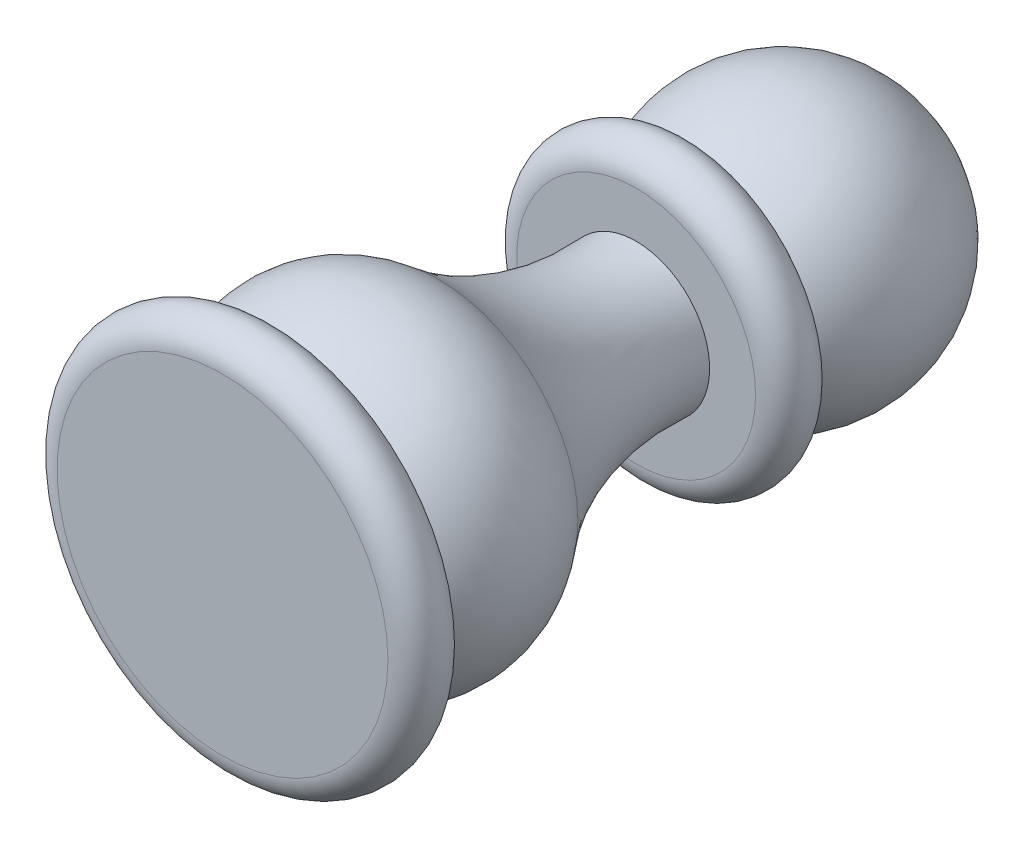
SolidWorks part; units mm, degrees
ref_plane "Front Plane" through (0, 0, 0) normal (0, 0, 1) x (1, 0, 0)
ref_plane "Top Plane" through (0, 0, 0) normal (0, 1, 0) x (1, 0, 0)
ref_plane "Right Plane" through (0, 0, 0) normal (1, 0, 0) x (0, 0, -1)
sketch "Sketch1" plane through (0, 0, 0) normal (0, 1, 0) x (1, 0, 0)
  line L0 (0, 0) -> (0, 22.5) construction
  line L1 (-9, 0) -> (0, 0) construction
  line L2 (-9, 1.5) -> (0, 1.5)
  line L3 (-9, -1.5) -> (0, -1.5)
  line L4 (-9, 0) -> (-9, 1.5) construction
  line L6 (-6.5, 1.5) -> (0, 1.5)
  line L7 (-6.5, 22.5) -> (0, 22.5) construction
  line L8 (-6.5, 24) -> (0, 24)
  line L9 (-6.5, 21) -> (0, 21)
  line L10 (0, 22.5) -> (0, 39.0485) construction
  line L11 (-4, 21) -> (0, 21)
  line L12 (0, -1.5) -> (0, 36.5)
  arc A0 (-9, 1.5) -> (-9, -1.5) centre (-9, 0) ccw
  arc A2 (0, 11.5695) -> (-6.5, 1.5) centre (-3, 6.3734) ccw
  arc A6 (-6.5, 24) -> (-6.5, 21) centre (-6.5, 22.5) ccw
  arc A8 (0, 36.5) -> (-5.5902, 24) centre (0, 29) ccw
  arc A9 (-7.5621, 10.2704) -> (-4.5071, 24) centre (-18.9675, 20.013) ccw
  arc A11 (0, 1.1772) -> (-0.5, 1.5) centre (3, 6.3734) cw
  point P5 (0, 0)
  point P17 (0, 22.5)
  dimension "D3" = 12
  dimension "D5" = 3
  dimension "D7" = 15
  dimension "D9" = 30
  dimension "D1" = 3
  dimension "D8" = 5
  dimension "D11" = 30.5
revolve "Revolve1" add sketch "Sketch1" angle 360 about L12
